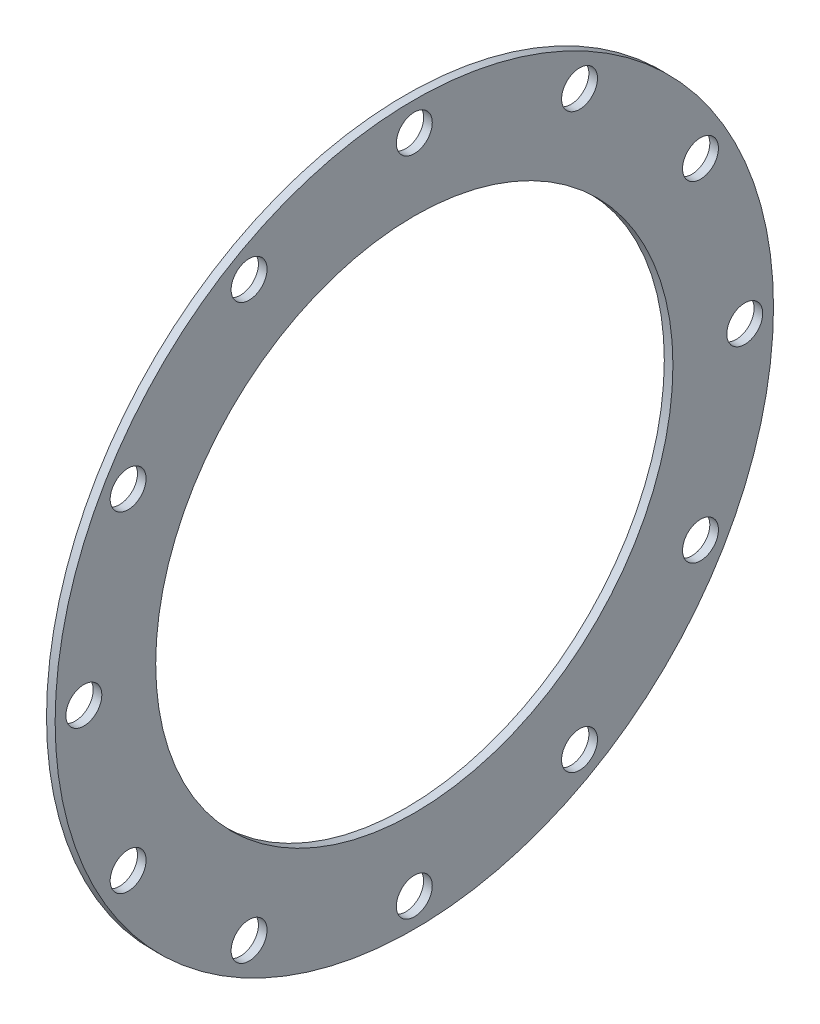
SolidWorks part; units mm, degrees
material "Silicon Rubber"
ref_plane "Front Plane" through (0, 0, 0) normal (0, 0, 1) x (1, 0, 0)
ref_plane "Top Plane" through (0, 0, 0) normal (0, 1, 0) x (1, 0, 0)
ref_plane "Right Plane" through (0, 0, 0) normal (1, 0, 0) x (0, 0, -1)
sketch "Sketch1" plane through (0, 0, 0) normal (1, 0, 0) x (0, 0, -1)
  circle A0 centre (0, 0) radius 2500
  circle A1 centre (0, 0) radius 2300 construction
  circle A2 centre (0, 2300) radius 125
  circle A3 centre (1150, 1991.8584) radius 125
  circle A4 centre (1991.8584, 1150) radius 125
  circle A5 centre (2300, 0) radius 125
  circle A6 centre (1991.8584, -1150) radius 125
  circle A7 centre (1150, -1991.8584) radius 125
  circle A8 centre (0, -2300) radius 125
  circle A9 centre (-1150, -1991.8584) radius 125
  circle A10 centre (-1991.8584, -1150) radius 125
  circle A11 centre (-2300, 0) radius 125
  circle A12 centre (-1991.8584, 1150) radius 125
  circle A13 centre (-1150, 1991.8584) radius 125
  point P30 (0, 0)
  dimension "D1" = 5000
  dimension "D2" = 12
extrude "Boss-Extrude1" add sketch "Sketch1" along normal blind 60
sketch "Sketch3" plane through (60, 0, 0) normal (1, 0, 0) x (0, 0, -1)
  circle A0 centre (0, 0) radius 1800
extrude "Cut-Extrude1" cut sketch "Sketch3" against normal blind 60
